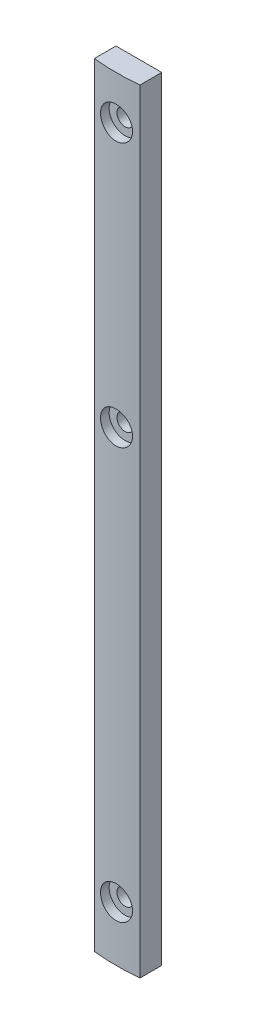
SolidWorks part; units mm, degrees
ref_plane "前视基准面" through (0, 0, 0) normal (0, 0, 1) x (1, 0, 0)
ref_plane "上视基准面" through (0, 0, 0) normal (0, 1, 0) x (1, 0, 0)
ref_plane "右视基准面" through (0, 0, 0) normal (1, 0, 0) x (0, 0, -1)
ref_plane "基准面4" through (0, 169, 0) normal (0, 1, 0) x (1, 0, 0)
sketch "草图1" plane through (0, 169, 0) normal (0, 1, 0) x (1, 0, 0)
  line L0 (1095, -2.4994) -> (1095, 2.25)
  line L1 (1095, 2.25) -> (1085, 2.25)
  line L2 (1085, 2.25) -> (1085, -2.4994)
  arc A0 (1085, -2.4994) -> (1095, -2.4994) centre (1090, 47.25) ccw
extrude "凸台-拉伸1" add sketch "草图1" against normal blind 169
hole_wizard "M3 六角头机械螺钉的柱形沉头孔1" positions "3D草图1" profile "草图2" counterbore size "M3" standard "ANSI Metric"
sketch3d "3D草图1"
  point P0 (1090, 101.825, 2.75)
  point P1 (1090, 159.5, 2.75)
  point P2 (1090, 12, 2.75)
  point P3 (0, 0, 0)
  point P4 (0, 0, 0)
sketch "草图2" plane through (1090, 101.825, 2.75) normal (1, 0, 0) x (0, -1, 0)
  line L0 (0, 0) -> (0, 5)
  line L1 (0, 5) -> (1.8, 5)
  line L3 (1.8, 5) -> (1.8, 2)
  line L4 (1.8, 2) -> (3.5, 2)
  line L5 (3.5, 2) -> (3.5, 0)
  line L7 (3.5, 0) -> (0, 0)
  line L11 (0, -6.35) -> (0, 107.95) construction
  dimension "通孔孔直径" = 3.6
  dimension "通孔孔深度" = 5
  dimension "柱形沉头孔直径" = 7
  dimension "柱形沉头孔深度" = 2
ref_plane "基准面5" through (1090, 0, 0) normal (1, 0, 0) x (0, 0, -1)
sketch "草图4" plane through (1090, 0, 0) normal (1, 0, 0) x (0, 0, -1)
  line L0 (-2.75, 159.5) -> (-2.75, 156)
  line L2 (-2.75, 156) -> (-0.75, 156)
  line L3 (-0.75, 156) -> (-0.75, 157.7)
  line L4 (-0.75, 157.7) -> (2.25, 157.7)
  line L5 (2.25, 157.7) -> (2.25, 159.5)
  line L6 (2.25, 159.5) -> (-2.75, 159.5)
sketch "草图5" plane through (1090, 0, 0) normal (1, 0, 0) x (0, 0, -1)
  line L0 (-2.75, 12) -> (-2.75, 8.5)
  line L1 (-2.75, 8.5) -> (-0.75, 8.5)
  line L2 (-2.75, 12) -> (2.25, 12)
  line L3 (2.25, 12) -> (2.25, 10.2)
  line L4 (2.25, 10.2) -> (-0.75, 10.2)
  line L5 (-0.75, 10.2) -> (-0.75, 8.5)
revolve "切除-旋转1" cut sketch "草图4" angle 360 about L6
revolve "切除-旋转2" cut sketch "草图5" angle 360 about L2
